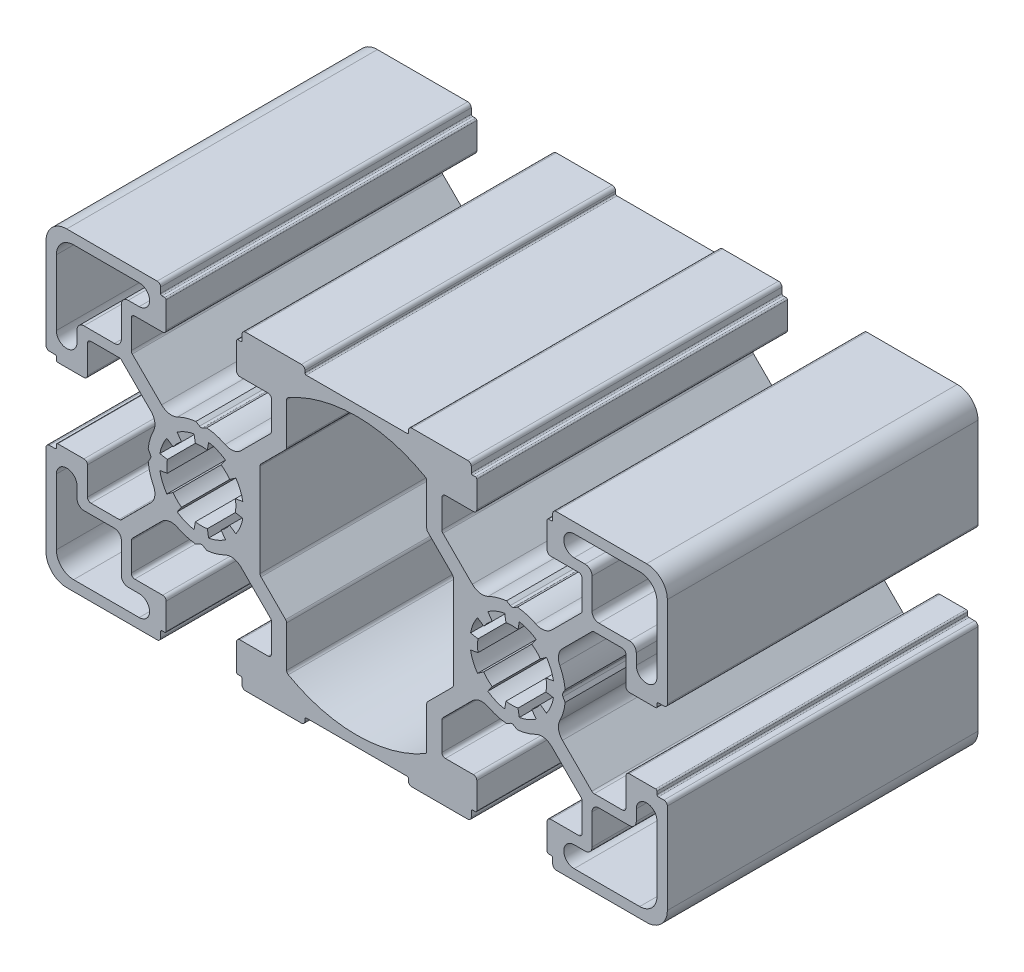
SolidWorks part; units mm, degrees
material "АД31Т ГОСТ 4784-97"
ref_plane "Спереди" through (0, 0, 0) normal (0, 0, 1) x (1, 0, 0)
ref_plane "Сверху" through (0, 0, 0) normal (0, 1, 0) x (1, 0, 0)
ref_plane "Справа" through (0, 0, 0) normal (1, 0, 0) x (0, 0, -1)
sketch "Эскиз1" plane through (0, 0, 0) normal (0, 0, 1) x (1, 0, 0)
  line L0 (61.1302, 38.6225) -> (61.1302, 41.3874)
  line L1 (55.1802, 50.121) -> (63.2802, 50.121)
  line L2 (37.1902, 42.2968) -> (37.1902, 40.211)
  line L3 (90.9123, 23.5252) -> (90.2814, 22.6242)
  line L4 (78.5802, 49.121) -> (63.9802, 49.121)
  line L6 (57.2802, 20.8838) -> (57.2802, 34.3583)
  line L7 (41.3945, 27.371) -> (41.0797, 26.8259)
  line L8 (45.9123, 31.7168) -> (45.2814, 32.6178)
  line L9 (32.2802, 33.221) -> (32.2802, 37.271)
  line L10 (32.7802, 37.771) -> (36.8675, 37.771)
  line L11 (26.7802, 33.521) -> (27.5802, 33.521)
  line L12 (27.9802, 32.721) -> (31.7802, 32.721)
  line L13 (27.7802, 33.321) -> (27.7802, 32.921)
  line L14 (26.7802, 33.521) -> (27.5802, 33.521)
  line L15 (52.876, 24.7531) -> (53.7771, 24.1222)
  line L16 (40.8924, 33.9532) -> (41.4723, 33.3733)
  line L17 (27.7802, 33.321) -> (27.7802, 32.921)
  line L18 (40.8924, 33.9532) -> (37.221, 37.6246)
  line L19 (48.5302, 35.0068) -> (47.9851, 35.3215)
  line L20 (26.2802, 34.021) -> (26.2802, 47.121)
  line L21 (51.6481, 23.5252) -> (52.279, 22.6242)
  line L22 (48.5302, 35.0068) -> (47.9851, 35.3215)
  line L23 (54.3802, 44.121) -> (58.4302, 44.121)
  line L24 (42.3802, 50.121) -> (29.2802, 50.121)
  line L25 (58.9302, 43.621) -> (58.9302, 39.5338)
  line L26 (42.448, 35.5089) -> (38.7767, 39.1802)
  line L27 (43.0802, 48.621) -> (43.4802, 48.621)
  line L28 (41.3945, 27.871) -> (41.0797, 28.4161)
  line L29 (42.448, 35.5089) -> (43.0279, 34.929)
  line L30 (42.8802, 49.621) -> (42.8802, 48.821)
  line L31 (43.0802, 48.621) -> (43.4802, 48.621)
  line L32 (43.6802, 48.421) -> (43.6802, 44.621)
  line L33 (42.8802, 49.621) -> (42.8802, 48.821)
  line L34 (38.6302, 43.621) -> (38.6302, 39.5338)
  line L35 (43.1802, 44.121) -> (39.1302, 44.121)
  line L36 (49.0302, 35.0068) -> (49.5753, 35.3215)
  line L37 (38.1902, 45.621) -> (39.7802, 45.621)
  line L38 (37.1902, 42.2968) -> (37.1902, 44.621)
  line L39 (27.7802, 46.121) -> (27.7802, 36.621)
  line L40 (54.6802, 49.621) -> (54.6802, 48.821)
  line L41 (34.1045, 39.211) -> (36.1902, 39.211)
  line L42 (34.1045, 39.211) -> (31.7802, 39.211)
  line L43 (30.7802, 38.211) -> (30.7802, 36.621)
  line L44 (53.8802, 48.421) -> (53.8802, 44.621)
  line L45 (30.2802, 48.621) -> (39.7802, 48.621)
  line L46 (54.4802, 48.621) -> (54.0802, 48.621)
  line L47 (54.6802, 49.621) -> (54.6802, 48.821)
  line L48 (55.1125, 35.5089) -> (54.5325, 34.929)
  line L49 (57.4267, 20.5302) -> (60.9838, 16.9731)
  line L50 (54.4802, 48.621) -> (54.0802, 48.621)
  line L51 (55.1125, 35.5089) -> (58.7838, 39.1802)
  line L52 (63.7802, 49.321) -> (63.7802, 49.621)
  line L53 (61.1302, 41.3874) -> (61.1302, 44.5658)
  line L54 (49.0302, 35.0068) -> (49.5753, 35.3215)
  line L55 (57.4267, 34.7118) -> (60.9838, 38.2689)
  line L56 (61.1302, 13.8546) -> (61.1302, 10.6762)
  line L57 (63.7802, 5.921) -> (63.7802, 5.621)
  line L58 (55.1125, 19.7331) -> (58.7838, 16.0618)
  line L59 (54.4802, 6.621) -> (54.0802, 6.621)
  line L60 (55.1125, 19.7331) -> (54.5325, 20.3131)
  line L61 (54.6802, 5.621) -> (54.6802, 6.421)
  line L62 (54.4802, 6.621) -> (54.0802, 6.621)
  line L63 (53.8802, 6.821) -> (53.8802, 10.621)
  line L64 (54.6802, 5.621) -> (54.6802, 6.421)
  line L65 (58.9302, 11.621) -> (58.9302, 15.7083)
  line L66 (54.3802, 11.121) -> (58.4302, 11.121)
  line L67 (78.5802, 6.121) -> (63.9802, 6.121)
  line L68 (55.1802, 5.121) -> (63.2802, 5.121)
  line L69 (61.1302, 16.6195) -> (61.1302, 13.8546)
  line L70 (89.6845, 24.7531) -> (88.7834, 24.1222)
  line L71 (88.8562, 26.7528) -> (87.7729, 26.5618)
  line L72 (88.8562, 28.4893) -> (87.7729, 28.6803)
  line L73 (89.6845, 30.4889) -> (88.7834, 31.1198)
  line L74 (90.9123, 31.7168) -> (90.2814, 32.6178)
  line L75 (98.7043, 28.4893) -> (99.7876, 28.6803)
  line L76 (49.0302, 20.2353) -> (49.5753, 19.9205)
  line L77 (98.7043, 26.7528) -> (99.7876, 26.5618)
  line L78 (97.876, 24.7531) -> (98.7771, 24.1222)
  line L79 (96.6481, 23.5252) -> (97.279, 22.6242)
  line L80 (94.6485, 22.697) -> (94.8395, 21.6137)
  line L81 (92.912, 22.697) -> (92.721, 21.6137)
  line L82 (55.1125, 19.7331) -> (54.5325, 20.3131)
  line L83 (98.7043, 28.4893) -> (99.7876, 28.6803)
  line L84 (98.7043, 26.7528) -> (99.7876, 26.5618)
  line L85 (30.2802, 6.621) -> (39.7802, 6.621)
  line L86 (92.912, 32.545) -> (92.721, 33.6283)
  line L87 (30.7802, 17.031) -> (30.7802, 18.621)
  line L88 (34.1045, 16.031) -> (31.7802, 16.031)
  line L89 (34.1045, 16.031) -> (36.1902, 16.031)
  line L90 (94.6485, 32.545) -> (94.8395, 33.6283)
  line L91 (27.7802, 9.121) -> (27.7802, 18.621)
  line L92 (37.1902, 12.9453) -> (37.1902, 10.621)
  line L93 (38.1902, 9.621) -> (39.7802, 9.621)
  line L94 (49.0302, 20.2353) -> (49.5753, 19.9205)
  line L95 (43.1802, 11.121) -> (39.1302, 11.121)
  line L96 (38.6302, 11.621) -> (38.6302, 15.7083)
  line L97 (42.8802, 5.621) -> (42.8802, 6.421)
  line L98 (43.6802, 6.821) -> (43.6802, 10.621)
  line L99 (43.0802, 6.621) -> (43.4802, 6.621)
  line L100 (42.8802, 5.621) -> (42.8802, 6.421)
  line L101 (42.448, 19.7331) -> (43.0279, 20.3131)
  line L102 (41.3945, 27.371) -> (41.0797, 26.8259)
  line L103 (43.0802, 6.621) -> (43.4802, 6.621)
  line L104 (42.448, 19.7331) -> (38.7767, 16.0618)
  line L105 (97.876, 30.4889) -> (98.7771, 31.1198)
  line L106 (42.3802, 5.121) -> (29.2802, 5.121)
  line L107 (105.3702, 12.9453) -> (105.3702, 15.031)
  line L108 (48.5302, 20.2353) -> (47.9851, 19.9205)
  line L109 (101.166, 27.871) -> (101.4807, 28.4161)
  line L110 (26.2802, 21.221) -> (26.2802, 8.121)
  line L111 (48.5302, 20.2353) -> (47.9851, 19.9205)
  line L112 (40.8924, 21.2888) -> (37.221, 17.6175)
  line L113 (27.7802, 21.921) -> (27.7802, 22.321)
  line L114 (40.8924, 21.2888) -> (41.4723, 21.8687)
  line L115 (110.2802, 22.021) -> (110.2802, 17.971)
  line L116 (26.7802, 21.721) -> (27.5802, 21.721)
  line L117 (27.7802, 21.921) -> (27.7802, 22.321)
  line L118 (27.9802, 22.521) -> (31.7802, 22.521)
  line L119 (26.7802, 21.721) -> (27.5802, 21.721)
  line L120 (32.7802, 17.471) -> (36.8675, 17.471)
  line L121 (32.2802, 22.021) -> (32.2802, 17.971)
  line L122 (41.3945, 27.871) -> (41.0797, 28.4161)
  line L123 (109.7802, 17.471) -> (105.693, 17.471)
  line L124 (115.7802, 21.721) -> (114.9802, 21.721)
  line L125 (114.5802, 22.521) -> (110.7802, 22.521)
  line L126 (114.7802, 21.921) -> (114.7802, 22.321)
  line L127 (37.1902, 12.9453) -> (37.1902, 15.031)
  line L128 (115.7802, 21.721) -> (114.9802, 21.721)
  line L129 (44.6845, 30.4889) -> (43.7834, 31.1198)
  line L130 (47.912, 32.545) -> (47.721, 33.6283)
  line L131 (49.6485, 32.545) -> (49.8395, 33.6283)
  line L132 (43.8562, 26.7528) -> (42.7729, 26.5618)
  line L133 (43.8562, 28.4893) -> (42.7729, 28.6803)
  line L134 (49.6485, 22.697) -> (49.8395, 21.6137)
  line L135 (47.912, 22.697) -> (47.721, 21.6137)
  line L136 (45.9123, 23.5252) -> (45.2814, 22.6242)
  line L137 (44.6845, 24.7531) -> (43.7834, 24.1222)
  line L138 (43.8562, 26.7528) -> (42.7729, 26.5618)
  line L139 (43.8562, 28.4893) -> (42.7729, 28.6803)
  line L140 (51.6481, 31.7168) -> (52.279, 32.6178)
  line L141 (52.876, 30.4889) -> (53.7771, 31.1198)
  line L142 (53.7043, 28.4893) -> (54.7876, 28.6803)
  line L143 (53.7043, 26.7528) -> (54.7876, 26.5618)
  line L144 (52.876, 24.7531) -> (53.7771, 24.1222)
  line L145 (51.6481, 23.5252) -> (52.279, 22.6242)
  line L146 (101.6681, 21.2888) -> (101.0882, 21.8687)
  line L147 (114.7802, 21.921) -> (114.7802, 22.321)
  line L148 (101.6681, 21.2888) -> (105.3394, 17.6175)
  line L149 (94.0302, 20.2353) -> (94.5753, 19.9205)
  line L150 (116.2802, 21.221) -> (116.2802, 8.121)
  line L151 (94.0302, 20.2353) -> (94.5753, 19.9205)
  line L152 (100.1802, 5.121) -> (113.2802, 5.121)
  line L153 (100.1125, 19.7331) -> (103.7838, 16.0618)
  line L154 (99.4802, 6.621) -> (99.0802, 6.621)
  line L155 (101.166, 27.371) -> (101.4807, 26.8259)
  line L156 (100.1125, 19.7331) -> (99.5325, 20.3131)
  line L157 (99.6802, 5.621) -> (99.6802, 6.421)
  line L158 (99.4802, 6.621) -> (99.0802, 6.621)
  line L159 (98.8802, 6.821) -> (98.8802, 10.621)
  line L160 (99.6802, 5.621) -> (99.6802, 6.421)
  line L161 (103.9302, 11.621) -> (103.9302, 15.7083)
  line L162 (99.3802, 11.121) -> (103.4302, 11.121)
  line L163 (93.5302, 20.2353) -> (92.9851, 19.9205)
  line L164 (104.3702, 9.621) -> (102.7802, 9.621)
  line L165 (105.3702, 12.9453) -> (105.3702, 10.621)
  line L166 (114.7802, 9.121) -> (114.7802, 18.621)
  line L167 (108.456, 16.031) -> (106.3702, 16.031)
  line L168 (108.456, 16.031) -> (110.7802, 16.031)
  line L169 (111.7802, 17.031) -> (111.7802, 18.621)
  line L170 (112.2802, 6.621) -> (102.7802, 6.621)
  line L171 (87.448, 19.7331) -> (88.0279, 20.3131)
  line L172 (93.5302, 20.2353) -> (92.9851, 19.9205)
  line L173 (81.4302, 16.6195) -> (81.4302, 13.8546)
  line L174 (87.3802, 5.121) -> (79.2802, 5.121)
  line L175 (88.1802, 11.121) -> (84.1302, 11.121)
  line L176 (83.6302, 11.621) -> (83.6302, 15.7083)
  line L177 (87.8802, 5.621) -> (87.8802, 6.421)
  line L178 (88.6802, 6.821) -> (88.6802, 10.621)
  line L179 (88.0802, 6.621) -> (88.4802, 6.621)
  line L180 (87.8802, 5.621) -> (87.8802, 6.421)
  line L181 (87.448, 19.7331) -> (88.0279, 20.3131)
  line L182 (88.0802, 6.621) -> (88.4802, 6.621)
  line L183 (87.448, 19.7331) -> (83.7767, 16.0618)
  line L184 (78.7802, 5.921) -> (78.7802, 5.621)
  line L185 (81.4302, 13.8546) -> (81.4302, 10.6762)
  line L186 (85.1338, 34.7118) -> (81.5767, 38.2689)
  line L187 (93.5302, 35.0068) -> (92.9851, 35.3215)
  line L188 (81.4302, 41.3874) -> (81.4302, 44.5658)
  line L189 (78.7802, 49.321) -> (78.7802, 49.621)
  line L190 (87.448, 35.5089) -> (83.7767, 39.1802)
  line L191 (88.0802, 48.621) -> (88.4802, 48.621)
  line L192 (85.1338, 20.5302) -> (81.5767, 16.9731)
  line L193 (87.448, 35.5089) -> (88.0279, 34.929)
  line L194 (87.8802, 49.621) -> (87.8802, 48.821)
  line L195 (88.0802, 48.621) -> (88.4802, 48.621)
  line L196 (112.2802, 48.621) -> (102.7802, 48.621)
  line L197 (88.6802, 48.421) -> (88.6802, 44.621)
  line L198 (111.7802, 38.211) -> (111.7802, 36.621)
  line L199 (108.456, 39.211) -> (110.7802, 39.211)
  line L200 (108.456, 39.211) -> (106.3702, 39.211)
  line L201 (87.8802, 49.621) -> (87.8802, 48.821)
  line L202 (114.7802, 46.121) -> (114.7802, 36.621)
  line L203 (105.3702, 42.2968) -> (105.3702, 44.621)
  line L204 (104.3702, 45.621) -> (102.7802, 45.621)
  line L205 (93.5302, 35.0068) -> (92.9851, 35.3215)
  line L206 (99.3802, 44.121) -> (103.4302, 44.121)
  line L207 (103.9302, 43.621) -> (103.9302, 39.5338)
  line L208 (99.6802, 49.621) -> (99.6802, 48.821)
  line L209 (98.8802, 48.421) -> (98.8802, 44.621)
  line L210 (99.4802, 48.621) -> (99.0802, 48.621)
  line L211 (99.6802, 49.621) -> (99.6802, 48.821)
  line L212 (100.1125, 35.5089) -> (99.5325, 34.929)
  line L213 (101.166, 27.871) -> (101.4807, 28.4161)
  line L214 (99.4802, 48.621) -> (99.0802, 48.621)
  line L215 (100.1125, 35.5089) -> (103.7838, 39.1802)
  line L216 (83.6302, 43.621) -> (83.6302, 39.5338)
  line L217 (100.1802, 50.121) -> (113.2802, 50.121)
  line L218 (88.1802, 44.121) -> (84.1302, 44.121)
  line L219 (94.0302, 35.0068) -> (94.5753, 35.3215)
  line L220 (90.9123, 23.5252) -> (90.2814, 22.6242)
  line L221 (116.2802, 34.021) -> (116.2802, 47.121)
  line L222 (94.0302, 35.0068) -> (94.5753, 35.3215)
  line L223 (101.6681, 33.9532) -> (105.3394, 37.6246)
  line L224 (114.7802, 33.321) -> (114.7802, 32.921)
  line L225 (101.6681, 33.9532) -> (101.0882, 33.3733)
  line L226 (89.6845, 24.7531) -> (88.7834, 24.1222)
  line L227 (115.7802, 33.521) -> (114.9802, 33.521)
  line L228 (114.7802, 33.321) -> (114.7802, 32.921)
  line L229 (114.5802, 32.721) -> (110.7802, 32.721)
  line L230 (115.7802, 33.521) -> (114.9802, 33.521)
  line L231 (109.7802, 37.771) -> (105.693, 37.771)
  line L232 (110.2802, 33.221) -> (110.2802, 37.271)
  line L233 (96.6481, 31.7168) -> (97.279, 32.6178)
  line L234 (101.166, 27.371) -> (101.4807, 26.8259)
  line L235 (85.2802, 20.8838) -> (85.2802, 34.3583)
  line L236 (105.3702, 42.2968) -> (105.3702, 40.211)
  line L237 (87.3802, 50.121) -> (79.2802, 50.121)
  line L238 (81.4302, 38.6225) -> (81.4302, 41.3874)
  arc A0 (45.9123, 31.7168) -> (44.6845, 30.4889) centre (48.7802, 27.621) ccw
  arc A1 (43.7834, 31.1198) -> (42.7729, 28.6803) centre (48.7802, 27.621) ccw
  arc A2 (29.2802, 50.121) -> (26.2802, 47.121) centre (29.2802, 47.121) ccw
  arc A3 (37.221, 37.6246) -> (36.8675, 37.771) centre (36.8675, 37.271) ccw
  arc A4 (32.7802, 37.771) -> (32.2802, 37.271) centre (32.7802, 37.271) ccw
  arc A5 (31.7802, 32.721) -> (32.2802, 33.221) centre (31.7802, 33.221) ccw
  arc A6 (26.2802, 34.021) -> (26.7802, 33.521) centre (26.7802, 34.021) ccw
  arc A7 (27.9802, 32.721) -> (27.7802, 32.921) centre (27.9802, 32.921) cw
  arc A8 (27.5802, 33.521) -> (27.7802, 33.321) centre (27.5802, 33.321) cw
  arc A9 (41.8488, 31.0685) -> (41.0797, 28.4161) centre (48.7802, 27.621) ccw
  arc A10 (61.3828, 45.0003) -> (61.1302, 44.5658) centre (61.6302, 44.5658) ccw
  arc A11 (81.1777, 45.0003) -> (61.3828, 45.0003) centre (71.2802, 27.621) ccw
  arc A12 (60.9838, 38.2689) -> (61.1302, 38.6225) centre (60.6302, 38.6225) ccw
  arc A13 (63.7802, 49.621) -> (63.2802, 50.121) centre (63.2802, 49.621) ccw
  arc A14 (57.2802, 34.3583) -> (57.4267, 34.7118) centre (57.7802, 34.3583) cw
  arc A15 (63.9802, 49.121) -> (63.7802, 49.321) centre (63.9802, 49.321) cw
  arc A16 (41.4723, 33.3733) -> (41.8488, 31.0685) centre (40.0581, 31.9591) cw
  arc A17 (42.8802, 48.821) -> (43.0802, 48.621) centre (43.0802, 48.821) ccw
  arc A18 (41.3945, 27.371) -> (41.3945, 27.871) centre (40.9615, 27.621) ccw
  arc A19 (26.2802, 34.021) -> (26.7802, 33.521) centre (26.7802, 34.021) ccw
  arc A20 (27.5802, 33.521) -> (27.7802, 33.321) centre (27.5802, 33.321) cw
  arc A21 (42.3802, 50.121) -> (42.8802, 49.621) centre (42.3802, 49.621) cw
  arc A22 (49.0302, 35.0068) -> (48.5302, 35.0068) centre (48.7802, 35.4398) cw
  arc A23 (43.0279, 34.929) -> (45.3328, 34.5524) centre (44.4421, 36.3432) ccw
  arc A24 (45.3328, 34.5524) -> (47.9851, 35.3215) centre (48.7802, 27.621) cw
  arc A25 (42.8802, 48.821) -> (43.0802, 48.621) centre (43.0802, 48.821) ccw
  arc A26 (43.6802, 48.421) -> (43.4802, 48.621) centre (43.4802, 48.421) ccw
  arc A27 (42.3802, 50.121) -> (42.8802, 49.621) centre (42.3802, 49.621) cw
  arc A28 (43.6802, 44.621) -> (43.1802, 44.121) centre (43.1802, 44.621) cw
  arc A29 (38.6302, 43.621) -> (39.1302, 44.121) centre (39.1302, 43.621) cw
  arc A30 (38.7767, 39.1802) -> (38.6302, 39.5338) centre (39.1302, 39.5338) cw
  arc A31 (27.7802, 46.121) -> (30.2802, 48.621) centre (30.2802, 46.121) cw
  arc A32 (27.7802, 36.621) -> (30.7802, 36.621) centre (29.2802, 36.621) ccw
  arc A33 (36.1902, 39.211) -> (37.1902, 40.211) centre (36.1902, 40.211) ccw
  arc A34 (31.7802, 39.211) -> (30.7802, 38.211) centre (31.7802, 38.211) ccw
  arc A35 (39.7802, 48.621) -> (39.7802, 45.621) centre (39.7802, 47.121) cw
  arc A36 (38.1902, 45.621) -> (37.1902, 44.621) centre (38.1902, 44.621) ccw
  arc A37 (58.7838, 39.1802) -> (58.9302, 39.5338) centre (58.4302, 39.5338) ccw
  arc A38 (58.9302, 43.621) -> (58.4302, 44.121) centre (58.4302, 43.621) ccw
  arc A39 (53.8802, 44.621) -> (54.3802, 44.121) centre (54.3802, 44.621) ccw
  arc A40 (55.1802, 50.121) -> (54.6802, 49.621) centre (55.1802, 49.621) ccw
  arc A41 (53.8802, 48.421) -> (54.0802, 48.621) centre (54.0802, 48.421) cw
  arc A42 (54.6802, 48.821) -> (54.4802, 48.621) centre (54.4802, 48.821) cw
  arc A43 (52.2277, 34.5524) -> (49.5753, 35.3215) centre (48.7802, 27.621) ccw
  arc A44 (54.5325, 34.929) -> (52.2277, 34.5524) centre (53.1183, 36.3432) cw
  arc A45 (55.1802, 50.121) -> (54.6802, 49.621) centre (55.1802, 49.621) ccw
  arc A46 (54.7876, 26.5618) -> (53.7771, 24.1222) centre (48.7802, 27.621) cw
  arc A47 (52.876, 24.7531) -> (51.6481, 23.5252) centre (48.7802, 27.621) cw
  arc A48 (52.279, 22.6242) -> (49.8395, 21.6137) centre (48.7802, 27.621) cw
  arc A49 (54.6802, 48.821) -> (54.4802, 48.621) centre (54.4802, 48.821) cw
  arc A50 (54.6802, 6.421) -> (54.4802, 6.621) centre (54.4802, 6.421) ccw
  arc A51 (55.1802, 5.121) -> (54.6802, 5.621) centre (55.1802, 5.621) cw
  arc A52 (54.5325, 20.3131) -> (52.2277, 20.6896) centre (53.1183, 18.8988) ccw
  arc A53 (52.2277, 20.6896) -> (49.5753, 19.9205) centre (48.7802, 27.621) cw
  arc A54 (54.6802, 6.421) -> (54.4802, 6.621) centre (54.4802, 6.421) ccw
  arc A55 (53.8802, 6.821) -> (54.0802, 6.621) centre (54.0802, 6.821) ccw
  arc A56 (55.1802, 5.121) -> (54.6802, 5.621) centre (55.1802, 5.621) cw
  arc A57 (53.8802, 10.621) -> (54.3802, 11.121) centre (54.3802, 10.621) cw
  arc A58 (58.9302, 11.621) -> (58.4302, 11.121) centre (58.4302, 11.621) cw
  arc A59 (58.7838, 16.0618) -> (58.9302, 15.7083) centre (58.4302, 15.7083) cw
  arc A60 (63.9802, 6.121) -> (63.7802, 5.921) centre (63.9802, 5.921) ccw
  arc A61 (57.2802, 20.8838) -> (57.4267, 20.5302) centre (57.7802, 20.8838) ccw
  arc A62 (63.7802, 5.621) -> (63.2802, 5.121) centre (63.2802, 5.621) cw
  arc A63 (60.9838, 16.9731) -> (61.1302, 16.6195) centre (60.6302, 16.6195) cw
  arc A64 (81.1777, 10.2417) -> (61.3828, 10.2417) centre (71.2802, 27.621) cw
  arc A65 (61.3828, 10.2417) -> (61.1302, 10.6762) centre (61.6302, 10.6762) cw
  arc A66 (99.7876, 26.5618) -> (98.7771, 24.1222) centre (93.7802, 27.621) cw
  arc A67 (98.7043, 28.4893) -> (98.7043, 26.7528) centre (93.7802, 27.621) cw
  arc A68 (97.279, 22.6242) -> (94.8395, 21.6137) centre (93.7802, 27.621) cw
  arc A69 (97.876, 24.7531) -> (96.6481, 23.5252) centre (93.7802, 27.621) cw
  arc A70 (92.721, 21.6137) -> (90.2814, 22.6242) centre (93.7802, 27.621) cw
  arc A71 (94.6485, 22.697) -> (92.912, 22.697) centre (93.7802, 27.621) cw
  arc A72 (54.5325, 20.3131) -> (52.2277, 20.6896) centre (53.1183, 18.8988) ccw
  arc A73 (52.2277, 20.6896) -> (49.5753, 19.9205) centre (48.7802, 27.621) cw
  arc A74 (88.7834, 24.1222) -> (87.7729, 26.5618) centre (93.7802, 27.621) cw
  arc A75 (90.9123, 23.5252) -> (89.6845, 24.7531) centre (93.7802, 27.621) cw
  arc A76 (87.7729, 28.6803) -> (88.7834, 31.1198) centre (93.7802, 27.621) cw
  arc A77 (88.8562, 26.7528) -> (88.8562, 28.4893) centre (93.7802, 27.621) cw
  arc A78 (89.6845, 30.4889) -> (90.9123, 31.7168) centre (93.7802, 27.621) cw
  arc A79 (90.2814, 32.6178) -> (92.721, 33.6283) centre (93.7802, 27.621) cw
  arc A80 (38.1902, 9.621) -> (37.1902, 10.621) centre (38.1902, 10.621) cw
  arc A81 (39.7802, 6.621) -> (39.7802, 9.621) centre (39.7802, 8.121) ccw
  arc A82 (31.7802, 16.031) -> (30.7802, 17.031) centre (31.7802, 17.031) cw
  arc A83 (36.1902, 16.031) -> (37.1902, 15.031) centre (36.1902, 15.031) cw
  arc A84 (27.7802, 18.621) -> (30.7802, 18.621) centre (29.2802, 18.621) cw
  arc A85 (27.7802, 9.121) -> (30.2802, 6.621) centre (30.2802, 9.121) ccw
  arc A86 (38.7767, 16.0618) -> (38.6302, 15.7083) centre (39.1302, 15.7083) ccw
  arc A87 (38.6302, 11.621) -> (39.1302, 11.121) centre (39.1302, 11.621) ccw
  arc A88 (43.6802, 10.621) -> (43.1802, 11.121) centre (43.1802, 10.621) ccw
  arc A89 (42.3802, 5.121) -> (42.8802, 5.621) centre (42.3802, 5.621) ccw
  arc A90 (43.6802, 6.821) -> (43.4802, 6.621) centre (43.4802, 6.821) cw
  arc A91 (42.8802, 6.421) -> (43.0802, 6.621) centre (43.0802, 6.421) cw
  arc A92 (45.3328, 20.6896) -> (47.9851, 19.9205) centre (48.7802, 27.621) ccw
  arc A93 (43.0279, 20.3131) -> (45.3328, 20.6896) centre (44.4421, 18.8988) cw
  arc A94 (49.0302, 20.2353) -> (48.5302, 20.2353) centre (48.7802, 19.8022) ccw
  arc A95 (42.3802, 5.121) -> (42.8802, 5.621) centre (42.3802, 5.621) ccw
  arc A96 (27.5802, 21.721) -> (27.7802, 21.921) centre (27.5802, 21.921) ccw
  arc A97 (26.2802, 21.221) -> (26.7802, 21.721) centre (26.7802, 21.221) cw
  arc A98 (42.8802, 6.421) -> (43.0802, 6.621) centre (43.0802, 6.421) cw
  arc A99 (41.4723, 21.8687) -> (41.8488, 24.1736) centre (40.0581, 23.2829) ccw
  arc A100 (92.912, 32.545) -> (94.6485, 32.545) centre (93.7802, 27.621) cw
  arc A101 (94.8395, 33.6283) -> (97.279, 32.6178) centre (93.7802, 27.621) cw
  arc A102 (113.2802, 5.121) -> (116.2802, 8.121) centre (113.2802, 8.121) ccw
  arc A103 (105.3394, 17.6175) -> (105.693, 17.471) centre (105.693, 17.971) ccw
  arc A104 (109.7802, 17.471) -> (110.2802, 17.971) centre (109.7802, 17.971) ccw
  arc A105 (110.7802, 22.521) -> (110.2802, 22.021) centre (110.7802, 22.021) ccw
  arc A106 (41.8488, 24.1736) -> (41.0797, 26.8259) centre (48.7802, 27.621) cw
  arc A107 (27.5802, 21.721) -> (27.7802, 21.921) centre (27.5802, 21.921) ccw
  arc A108 (27.9802, 22.521) -> (27.7802, 22.321) centre (27.9802, 22.321) ccw
  arc A109 (26.2802, 21.221) -> (26.7802, 21.721) centre (26.7802, 21.221) cw
  arc A110 (31.7802, 22.521) -> (32.2802, 22.021) centre (31.7802, 22.021) cw
  arc A111 (32.7802, 17.471) -> (32.2802, 17.971) centre (32.7802, 17.971) cw
  arc A112 (37.221, 17.6175) -> (36.8675, 17.471) centre (36.8675, 17.971) cw
  arc A113 (29.2802, 5.121) -> (26.2802, 8.121) centre (29.2802, 8.121) cw
  arc A114 (47.721, 33.6283) -> (45.2814, 32.6178) centre (48.7802, 27.621) ccw
  arc A115 (49.6485, 32.545) -> (47.912, 32.545) centre (48.7802, 27.621) ccw
  arc A116 (52.279, 32.6178) -> (49.8395, 33.6283) centre (48.7802, 27.621) ccw
  arc A117 (52.876, 30.4889) -> (51.6481, 31.7168) centre (48.7802, 27.621) ccw
  arc A118 (53.7043, 26.7528) -> (53.7043, 28.4893) centre (48.7802, 27.621) ccw
  arc A119 (54.7876, 28.6803) -> (53.7771, 31.1198) centre (48.7802, 27.621) ccw
  arc A120 (51.6481, 23.5252) -> (52.876, 24.7531) centre (48.7802, 27.621) ccw
  arc A121 (53.7771, 24.1222) -> (54.7876, 26.5618) centre (48.7802, 27.621) ccw
  arc A122 (47.912, 22.697) -> (49.6485, 22.697) centre (48.7802, 27.621) ccw
  arc A123 (49.8395, 21.6137) -> (52.279, 22.6242) centre (48.7802, 27.621) ccw
  arc A124 (44.6845, 24.7531) -> (45.9123, 23.5252) centre (48.7802, 27.621) ccw
  arc A125 (45.2814, 22.6242) -> (47.721, 21.6137) centre (48.7802, 27.621) ccw
  arc A126 (43.8562, 28.4893) -> (43.8562, 26.7528) centre (48.7802, 27.621) ccw
  arc A127 (42.7729, 26.5618) -> (43.7834, 24.1222) centre (48.7802, 27.621) ccw
  arc A128 (116.2802, 21.221) -> (115.7802, 21.721) centre (115.7802, 21.221) ccw
  arc A129 (114.5802, 22.521) -> (114.7802, 22.321) centre (114.5802, 22.321) cw
  arc A130 (114.9802, 21.721) -> (114.7802, 21.921) centre (114.9802, 21.921) cw
  arc A131 (100.7117, 24.1736) -> (101.4807, 26.8259) centre (93.7802, 27.621) ccw
  arc A132 (101.0882, 21.8687) -> (100.7117, 24.1736) centre (102.5024, 23.2829) cw
  arc A133 (99.6802, 6.421) -> (99.4802, 6.621) centre (99.4802, 6.421) ccw
  arc A134 (116.2802, 21.221) -> (115.7802, 21.721) centre (115.7802, 21.221) ccw
  arc A135 (114.9802, 21.721) -> (114.7802, 21.921) centre (114.9802, 21.921) cw
  arc A136 (100.1802, 5.121) -> (99.6802, 5.621) centre (100.1802, 5.621) cw
  arc A137 (93.5302, 20.2353) -> (94.0302, 20.2353) centre (93.7802, 19.8022) cw
  arc A138 (99.5325, 20.3131) -> (97.2277, 20.6896) centre (98.1183, 18.8988) ccw
  arc A139 (97.2277, 20.6896) -> (94.5753, 19.9205) centre (93.7802, 27.621) cw
  arc A140 (99.6802, 6.421) -> (99.4802, 6.621) centre (99.4802, 6.421) ccw
  arc A141 (98.8802, 6.821) -> (99.0802, 6.621) centre (99.0802, 6.821) ccw
  arc A142 (100.1802, 5.121) -> (99.6802, 5.621) centre (100.1802, 5.621) cw
  arc A143 (98.8802, 10.621) -> (99.3802, 11.121) centre (99.3802, 10.621) cw
  arc A144 (103.9302, 11.621) -> (103.4302, 11.121) centre (103.4302, 11.621) cw
  arc A145 (103.7838, 16.0618) -> (103.9302, 15.7083) centre (103.4302, 15.7083) cw
  arc A146 (114.7802, 9.121) -> (112.2802, 6.621) centre (112.2802, 9.121) cw
  arc A147 (114.7802, 18.621) -> (111.7802, 18.621) centre (113.2802, 18.621) ccw
  arc A148 (106.3702, 16.031) -> (105.3702, 15.031) centre (106.3702, 15.031) ccw
  arc A149 (110.7802, 16.031) -> (111.7802, 17.031) centre (110.7802, 17.031) ccw
  arc A150 (102.7802, 6.621) -> (102.7802, 9.621) centre (102.7802, 8.121) cw
  arc A151 (104.3702, 9.621) -> (105.3702, 10.621) centre (104.3702, 10.621) ccw
  arc A152 (90.3328, 20.6896) -> (92.9851, 19.9205) centre (93.7802, 27.621) ccw
  arc A153 (88.0279, 20.3131) -> (90.3328, 20.6896) centre (89.4421, 18.8988) cw
  arc A154 (81.1777, 10.2417) -> (81.4302, 10.6762) centre (80.9302, 10.6762) ccw
  arc A155 (81.5767, 16.9731) -> (81.4302, 16.6195) centre (81.9302, 16.6195) ccw
  arc A156 (78.7802, 5.621) -> (79.2802, 5.121) centre (79.2802, 5.621) ccw
  arc A157 (85.2802, 20.8838) -> (85.1338, 20.5302) centre (84.7802, 20.8838) cw
  arc A158 (78.5802, 6.121) -> (78.7802, 5.921) centre (78.5802, 5.921) cw
  arc A159 (83.7767, 16.0618) -> (83.6302, 15.7083) centre (84.1302, 15.7083) ccw
  arc A160 (83.6302, 11.621) -> (84.1302, 11.121) centre (84.1302, 11.621) ccw
  arc A161 (88.6802, 10.621) -> (88.1802, 11.121) centre (88.1802, 10.621) ccw
  arc A162 (87.3802, 5.121) -> (87.8802, 5.621) centre (87.3802, 5.621) ccw
  arc A163 (88.6802, 6.821) -> (88.4802, 6.621) centre (88.4802, 6.821) cw
  arc A164 (87.8802, 6.421) -> (88.0802, 6.621) centre (88.0802, 6.421) cw
  arc A165 (90.3328, 20.6896) -> (92.9851, 19.9205) centre (93.7802, 27.621) ccw
  arc A166 (88.0279, 20.3131) -> (90.3328, 20.6896) centre (89.4421, 18.8988) cw
  arc A167 (87.3802, 5.121) -> (87.8802, 5.621) centre (87.3802, 5.621) ccw
  arc A168 (87.8802, 6.421) -> (88.0802, 6.621) centre (88.0802, 6.421) cw
  arc A169 (87.8802, 48.821) -> (88.0802, 48.621) centre (88.0802, 48.821) ccw
  arc A170 (90.2814, 22.6242) -> (92.721, 21.6137) centre (93.7802, 27.621) ccw
  arc A171 (89.6845, 24.7531) -> (90.9123, 23.5252) centre (93.7802, 27.621) ccw
  arc A172 (87.7729, 26.5618) -> (88.7834, 24.1222) centre (93.7802, 27.621) ccw
  arc A173 (87.3802, 50.121) -> (87.8802, 49.621) centre (87.3802, 49.621) cw
  arc A174 (88.0279, 34.929) -> (90.3328, 34.5524) centre (89.4421, 36.3432) ccw
  arc A175 (90.3328, 34.5524) -> (92.9851, 35.3215) centre (93.7802, 27.621) cw
  arc A176 (87.8802, 48.821) -> (88.0802, 48.621) centre (88.0802, 48.821) ccw
  arc A177 (88.6802, 48.421) -> (88.4802, 48.621) centre (88.4802, 48.421) ccw
  arc A178 (87.3802, 50.121) -> (87.8802, 49.621) centre (87.3802, 49.621) cw
  arc A179 (88.6802, 44.621) -> (88.1802, 44.121) centre (88.1802, 44.621) cw
  arc A180 (83.6302, 43.621) -> (84.1302, 44.121) centre (84.1302, 43.621) cw
  arc A181 (83.7767, 39.1802) -> (83.6302, 39.5338) centre (84.1302, 39.5338) cw
  arc A182 (104.3702, 45.621) -> (105.3702, 44.621) centre (104.3702, 44.621) cw
  arc A183 (102.7802, 48.621) -> (102.7802, 45.621) centre (102.7802, 47.121) ccw
  arc A184 (110.7802, 39.211) -> (111.7802, 38.211) centre (110.7802, 38.211) cw
  arc A185 (106.3702, 39.211) -> (105.3702, 40.211) centre (106.3702, 40.211) cw
  arc A186 (114.7802, 36.621) -> (111.7802, 36.621) centre (113.2802, 36.621) cw
  arc A187 (114.7802, 46.121) -> (112.2802, 48.621) centre (112.2802, 46.121) ccw
  arc A188 (103.7838, 39.1802) -> (103.9302, 39.5338) centre (103.4302, 39.5338) ccw
  arc A189 (103.9302, 43.621) -> (103.4302, 44.121) centre (103.4302, 43.621) ccw
  arc A190 (98.8802, 44.621) -> (99.3802, 44.121) centre (99.3802, 44.621) ccw
  arc A191 (100.1802, 50.121) -> (99.6802, 49.621) centre (100.1802, 49.621) ccw
  arc A192 (98.8802, 48.421) -> (99.0802, 48.621) centre (99.0802, 48.421) cw
  arc A193 (99.6802, 48.821) -> (99.4802, 48.621) centre (99.4802, 48.821) cw
  arc A194 (97.2277, 34.5524) -> (94.5753, 35.3215) centre (93.7802, 27.621) ccw
  arc A195 (99.5325, 34.929) -> (97.2277, 34.5524) centre (98.1183, 36.3432) cw
  arc A196 (93.5302, 35.0068) -> (94.0302, 35.0068) centre (93.7802, 35.4398) ccw
  arc A197 (100.1802, 50.121) -> (99.6802, 49.621) centre (100.1802, 49.621) ccw
  arc A198 (114.9802, 33.521) -> (114.7802, 33.321) centre (114.9802, 33.321) ccw
  arc A199 (116.2802, 34.021) -> (115.7802, 33.521) centre (115.7802, 34.021) cw
  arc A200 (101.166, 27.371) -> (101.166, 27.871) centre (101.599, 27.621) cw
  arc A201 (99.6802, 48.821) -> (99.4802, 48.621) centre (99.4802, 48.821) cw
  arc A202 (101.0882, 33.3733) -> (100.7117, 31.0685) centre (102.5024, 31.9591) ccw
  arc A203 (78.5802, 49.121) -> (78.7802, 49.321) centre (78.5802, 49.321) ccw
  arc A204 (85.2802, 34.3583) -> (85.1338, 34.7118) centre (84.7802, 34.3583) ccw
  arc A205 (78.7802, 49.621) -> (79.2802, 50.121) centre (79.2802, 49.621) cw
  arc A206 (81.5767, 38.2689) -> (81.4302, 38.6225) centre (81.9302, 38.6225) cw
  arc A207 (81.1777, 45.0003) -> (81.4302, 44.5658) centre (80.9302, 44.5658) cw
  arc A208 (100.7117, 31.0685) -> (101.4807, 28.4161) centre (93.7802, 27.621) cw
  arc A209 (114.9802, 33.521) -> (114.7802, 33.321) centre (114.9802, 33.321) ccw
  arc A210 (114.5802, 32.721) -> (114.7802, 32.921) centre (114.5802, 32.921) ccw
  arc A211 (116.2802, 34.021) -> (115.7802, 33.521) centre (115.7802, 34.021) cw
  arc A212 (110.7802, 32.721) -> (110.2802, 33.221) centre (110.7802, 33.221) cw
  arc A213 (109.7802, 37.771) -> (110.2802, 37.271) centre (109.7802, 37.271) cw
  arc A214 (105.3394, 37.6246) -> (105.693, 37.771) centre (105.693, 37.271) cw
  arc A215 (113.2802, 50.121) -> (116.2802, 47.121) centre (113.2802, 47.121) cw
  arc A216 (98.7771, 31.1198) -> (99.7876, 28.6803) centre (93.7802, 27.621) cw
  arc A217 (96.6481, 31.7168) -> (97.876, 30.4889) centre (93.7802, 27.621) cw
  point P62 (41.0388, 26.755)
  point P65 (41.0388, 28.487)
  point P69 (26.2802, 33.521)
  point P92 (42.8802, 50.121)
  point P93 (47.9142, 35.3624)
  point P94 (49.6462, 35.3624)
  point P164 (54.6802, 50.121)
  point P170 (54.6802, 5.121)
  point P308 (49.6462, 19.8796)
  point P309 (47.9142, 19.8796)
  point P310 (42.8802, 5.121)
  point P311 (26.2802, 21.721)
  point P528 (71.2802, 6.121)
  point P534 (116.2802, 21.721)
  point P535 (99.6802, 5.121)
  point P536 (94.6462, 19.8796)
  point P537 (92.9142, 19.8796)
  point P538 (87.8802, 5.121)
  point P539 (87.8802, 50.121)
  point P540 (92.9142, 35.3624)
  point P541 (94.6462, 35.3624)
  point P542 (99.6802, 50.121)
  point P543 (116.2802, 33.521)
  point P544 (101.5216, 28.487)
  point P545 (101.5216, 26.755)
extrude "Бобышка-Вытянуть1" add sketch "Эскиз1" along normal blind 45 contours A215 L217 A191 L208 A193 L210 A192 L209 A190 L206 A189 L207 A188 L215 L212 A195 A194 L219 A196 L187 A175 A174 L193 L190 A181 L216 A180 L218 A179 L197 A177 L191 A169 L194 A173 L237 A205 L189 A203 L4 A15 L52 A13 L1 A40 L40 A42 L46 A41 L44 A39
